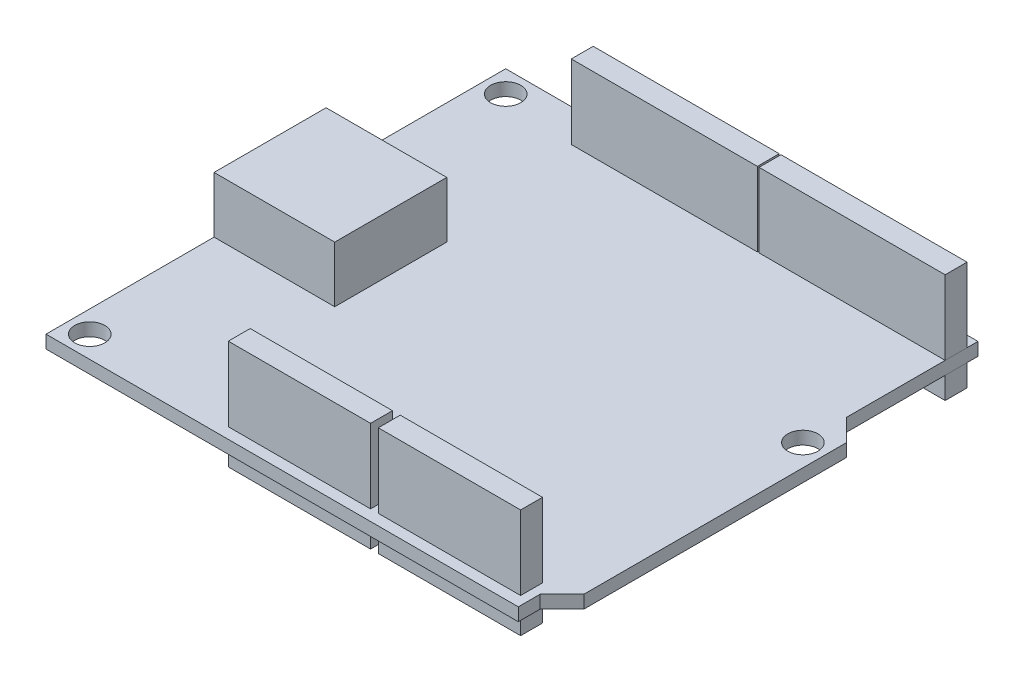
SolidWorks part; units mm, degrees
ref_plane "Front Plane" through (0, 0, 0) normal (0, 0, 1) x (1, 0, 0)
ref_plane "Top Plane" through (0, 0, 0) normal (0, 1, 0) x (1, 0, 0)
ref_plane "Right Plane" through (0, 0, 0) normal (1, 0, 0) x (0, 0, -1)
sketch "Sketch1" plane through (0, 0, 0) normal (0, 1, 0) x (1, 0, 0)
  line L0 (-27.4, -26.67) -> (27.4, 26.67) construction
  line L1 (-27.4, -26.67) -> (27.4, -26.67)
  line L2 (-27.4, -26.67) -> (-27.4, 26.67)
  line L3 (-27.4, 26.67) -> (27.4, 26.67)
  line L4 (27.4, -26.67) -> (27.4, -24.13)
  line L5 (27.4, -24.13) -> (29.94, -21.59)
  line L6 (29.94, -21.59) -> (29.94, 8.89)
  line L7 (29.94, 8.89) -> (27.4, 11.43)
  line L8 (27.4, 11.43) -> (27.4, 26.67)
  dimension "D1" = 54.8
  dimension "D2" = 53.34
  dimension "D3" = 2.54
  dimension "D4" = 2.54
  dimension "D5" = 35.56
extrude "Boss-Extrude1" add sketch "Sketch1" along normal blind 1.5
sketch "Sketch2" plane through (0, 1.5, 0) normal (0, 1, 0) x (1, 0, 0)
  line L0 (-24.86, 24.13) -> (-27.4, 24.13) construction
  line L1 (-27.4, 26.67) -> (-27.4, -26.67) construction
  line L2 (-24.86, 24.13) -> (-24.86, 26.67) construction
  line L3 (27.4, 26.67) -> (-27.4, 26.67) construction
  line L4 (-24.86, -24.13) -> (-27.4, -24.13) construction
  line L5 (-24.86, -24.13) -> (-24.86, -26.67) construction
  line L6 (-27.4, -26.67) -> (27.4, -26.67) construction
  line L7 (27.4, 6.35) -> (29.94, 6.35) construction
  line L8 (29.94, -21.59) -> (29.94, 8.89) construction
  line L9 (27.4, 6.35) -> (27.4, 11.43) construction
  circle A0 centre (-24.86, -24.13) radius 1.75
  circle A1 centre (-24.86, 24.13) radius 1.75
  circle A2 centre (27.4, 6.35) radius 1.75
  dimension "D1" = 3.5
  dimension "D2" = 2.54
  dimension "D3" = 5.08
extrude "Cut-Extrude1" cut sketch "Sketch2" against normal through all
sketch "Sketch3" plane through (0, 1.5, 0) normal (0, 1, 0) x (1, 0, 0)
  line L0 (-27.4, 26.67) -> (-27.4, -26.67) construction
  line L1 (-27.4, 5.83) -> (-13.4, 5.83)
  line L2 (-27.4, 5.83) -> (-27.4, -7.17)
  line L3 (-27.4, -7.17) -> (-13.4, -7.17)
  line L4 (-13.4, 5.83) -> (-13.4, -7.17)
  line L5 (-27.4, -26.67) -> (27.4, -26.67) construction
  dimension "D1" = 14
  dimension "D2" = 13
  dimension "D3" = 19.5
extrude "Boss-Extrude2" add sketch "Sketch3" along normal blind 6.5 separate body
sketch "Sketch4" plane through (0, 1.5, 0) normal (0, 1, 0) x (1, 0, 0)
  line L1 (-7.52, -22.86) -> (8.99, -22.86)
  line L2 (-7.52, -22.86) -> (-7.52, -25.4)
  line L3 (-7.52, -25.4) -> (8.99, -25.4)
  line L4 (8.99, -22.86) -> (8.99, -25.4)
  line L5 (9.89, -22.86) -> (26.4, -22.86)
  line L6 (9.89, -22.86) -> (9.89, -25.4)
  line L7 (9.89, -25.4) -> (26.4, -25.4)
  line L8 (26.4, -22.86) -> (26.4, -25.4)
  line L9 (-15.981, 25.4) -> (5.609, 25.4)
  line L10 (-15.981, 25.4) -> (-15.981, 22.86)
  line L11 (-15.981, 22.86) -> (5.609, 22.86)
  line L12 (5.609, 25.4) -> (5.609, 22.86)
  line L13 (5.809, 25.4) -> (27.399, 25.4)
  line L14 (5.809, 25.4) -> (5.809, 22.86)
  line L15 (5.809, 22.86) -> (27.399, 22.86)
  line L16 (27.399, 25.4) -> (27.399, 22.86)
  line L17 (27.4, 26.67) -> (-27.4, 26.67) construction
  line L18 (-27.4, -26.67) -> (27.4, -26.67) construction
  line L19 (27.4, -26.67) -> (27.4, -24.13) construction
  line L20 (27.4, 11.43) -> (27.4, 26.67) construction
  dimension "D1" = 2.54
  dimension "D2" = 21.59
  dimension "D3" = 1.27
  dimension "D4" = 0.2
  dimension "D5" = 1.27
  dimension "D6" = 16.51
  dimension "D7" = 1
  dimension "D8" = 0.9
  dimension "D9" = 0.001
extrude "Boss-Extrude3" add sketch "Sketch4" along normal blind 8.6 and the other way blind 4.04 separate body
